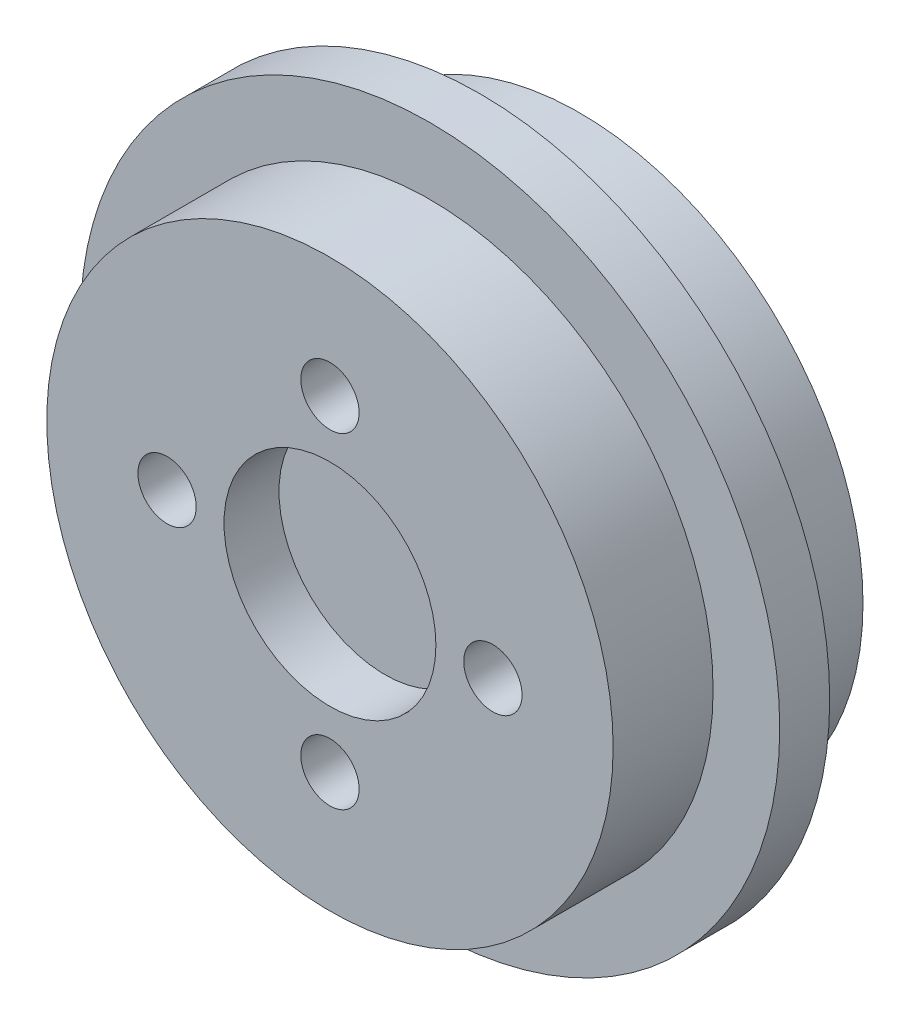
SolidWorks part; units mm, degrees
ref_plane "Front Plane" through (0, 0, 0) normal (0, 0, 1) x (1, 0, 0)
ref_plane "Top Plane" through (0, 0, 0) normal (0, 1, 0) x (1, 0, 0)
ref_plane "Right Plane" through (0, 0, 0) normal (1, 0, 0) x (0, 0, -1)
sketch "Sketch1" plane through (0, 0, 0) normal (0, 0, 1) x (1, 0, 0)
  circle A0 centre (0, 0) radius 17
  dimension "D1" = 34
extrude "Boss-Extrude1" add sketch "Sketch1" along normal blind 15
sketch "Sketch2" plane through (0, 0, 0) normal (0, 0, -1) x (-1, 0, 0)
  line L0 (0, 14.35) -> (0, 9.1782) construction
  line L1 (1.15, 14.35) -> (1.15, 9.1782)
  line L2 (-1.15, 14.35) -> (-1.15, 9.1782)
  line L3 (9.3338, 10.9602) -> (5.6768, 7.3032)
  line L4 (10.9602, 9.3338) -> (7.3032, 5.6768)
  line L5 (10.147, 10.147) -> (6.49, 6.49) construction
  line L6 (14.35, 1.15) -> (9.1782, 1.15)
  line L7 (14.35, -1.15) -> (9.1782, -1.15)
  line L8 (14.35, 0) -> (9.1782, 0) construction
  line L9 (10.9602, -9.3338) -> (7.3032, -5.6768)
  line L10 (9.3338, -10.9602) -> (5.6768, -7.3032)
  line L11 (10.147, -10.147) -> (6.49, -6.49) construction
  line L12 (1.15, -14.35) -> (1.15, -9.1782)
  line L13 (-1.15, -14.35) -> (-1.15, -9.1782)
  line L14 (0, -14.35) -> (0, -9.1782) construction
  line L15 (-9.3338, -10.9602) -> (-5.6768, -7.3032)
  line L16 (-10.9602, -9.3338) -> (-7.3032, -5.6768)
  line L17 (-10.147, -10.147) -> (-6.49, -6.49) construction
  line L18 (-14.35, -1.15) -> (-9.1782, -1.15)
  line L19 (-14.35, 1.15) -> (-9.1782, 1.15)
  line L20 (-14.35, 0) -> (-9.1782, 0) construction
  line L21 (-10.9602, 9.3338) -> (-7.3032, 5.6768)
  line L22 (-9.3338, 10.9602) -> (-5.6768, 7.3032)
  line L23 (-10.147, 10.147) -> (-6.49, 6.49) construction
  circle A0 centre (0, 0) radius 9.25
  circle A1 centre (0, 0) radius 15.5 construction
  arc A2 (1.15, 14.35) -> (-1.15, 14.35) centre (0, 14.35) ccw
  arc A3 (-1.15, 9.1782) -> (1.15, 9.1782) centre (0, 9.1782) ccw
  arc A4 (10.9602, 9.3338) -> (9.3338, 10.9602) centre (10.147, 10.147) ccw
  arc A5 (5.6768, 7.3032) -> (7.3032, 5.6768) centre (6.49, 6.49) ccw
  arc A6 (14.35, -1.15) -> (14.35, 1.15) centre (14.35, 0) ccw
  arc A7 (9.1782, 1.15) -> (9.1782, -1.15) centre (9.1782, 0) ccw
  arc A8 (9.3338, -10.9602) -> (10.9602, -9.3338) centre (10.147, -10.147) ccw
  arc A9 (7.3032, -5.6768) -> (5.6768, -7.3032) centre (6.49, -6.49) ccw
  arc A10 (-1.15, -14.35) -> (1.15, -14.35) centre (0, -14.35) ccw
  arc A11 (1.15, -9.1782) -> (-1.15, -9.1782) centre (0, -9.1782) ccw
  arc A12 (-10.9602, -9.3338) -> (-9.3338, -10.9602) centre (-10.147, -10.147) ccw
  arc A13 (-5.6768, -7.3032) -> (-7.3032, -5.6768) centre (-6.49, -6.49) ccw
  arc A14 (-14.35, 1.15) -> (-14.35, -1.15) centre (-14.35, 0) ccw
  arc A15 (-9.1782, -1.15) -> (-9.1782, 1.15) centre (-9.1782, 0) ccw
  arc A16 (-9.3338, 10.9602) -> (-10.9602, 9.3338) centre (-10.147, 10.147) ccw
  arc A17 (-7.3032, 5.6768) -> (-5.6768, 7.3032) centre (-6.49, 6.49) ccw
  point P6 (0, 11.7641)
  point P15 (8.3185, 8.3185)
  point P22 (11.7641, 0)
  point P29 (8.3185, -8.3185)
  point P36 (0, -11.7641)
  point P43 (-8.3185, -8.3185)
  point P50 (-11.7641, 0)
  point P57 (-8.3185, 8.3185)
  point P62 (0, 0)
  dimension "D1" = 18.5
  dimension "D2" = 31
  dimension "D3" = 2.3
  dimension "D4" = 8
extrude "Cut-Extrude2" cut sketch "Sketch2" against normal blind 5 contours A17 A0 A15 A13 A11 A9 A7 A5 A3 | L4 A4 L3 A0 | L7 A6 L6 A0 | L10 A8 L9 A0 | L13 A10 L12 A0 | L16 A12 L15 A0 | L19 A14 L18 A0 | L22 A16 L21 A0 | L1 A2 L2 A0 | A0 A9 | A0 A3 | A0 A5 | A0 A7 | A0 A11 | A0 A13 | A0 A15 | A0 A17
sketch "Sketch3" plane through (0, 0, 15) normal (0, 0, 1) x (1, 0, 0)
  circle A1 centre (0, 0) radius 9.78 construction
  circle A2 centre (0, 9.78) radius 1.75
  circle A3 centre (9.78, 0) radius 1.75
  circle A4 centre (0, -9.78) radius 1.75
  circle A5 centre (-9.78, 0) radius 1.75
  point P15 (0, 0)
  dimension "D2" = 19.56
  dimension "D3" = 3.5
  dimension "D4" = 4
extrude "Cut-Extrude3" cut sketch "Sketch3" against normal blind 5
sketch "Sketch4" plane through (0, 0, 0) normal (1, 0, 0) x (0, 0, -1)
  line L0 (-15, -17) -> (-7, -17) construction
  line L1 (-9, -17) -> (-6, -17)
  line L2 (-9, -17) -> (-9, -21)
  line L3 (-9, -21) -> (-6, -21)
  line L4 (-6, -17) -> (-6, -21)
  line L5 (0, -17) -> (0, 17) construction
  line L6 (-20.3756, 0) -> (6.8872, 0) construction
  dimension "D1" = 6
  dimension "D2" = 3
  dimension "D3" = 4
revolve "Revolve1" add sketch "Sketch4" angle 360 about L6
sketch "Sketch5" plane through (0, 0, 15) normal (0, 0, 1) x (1, 0, 0)
  circle A0 centre (0, 0) radius 6.36
  dimension "D1" = 12.72
extrude "Cut-Extrude4" cut sketch "Sketch5" against normal blind 3.3
